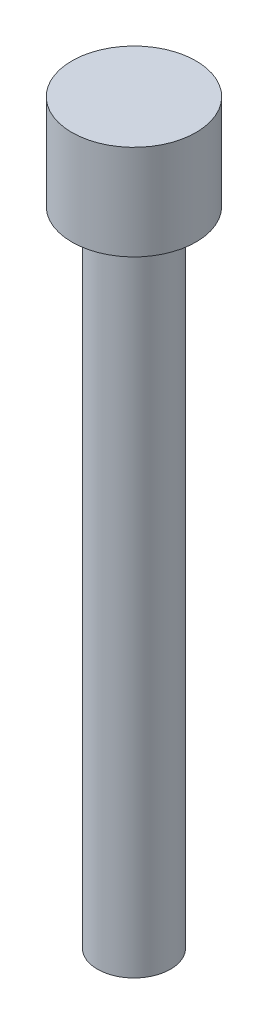
SolidWorks part; units mm, degrees
ref_plane "Front Plane" through (0, 0, 0) normal (0, 0, 1) x (1, 0, 0)
ref_plane "Top Plane" through (0, 0, 0) normal (0, 1, 0) x (1, 0, 0)
ref_plane "Right Plane" through (0, 0, 0) normal (1, 0, 0) x (0, 0, -1)
sketch "Sketch1" plane through (0, 0, 0) normal (0, 1, 0) x (1, 0, 0)
  circle A0 centre (0, 0) radius 2.5
  dimension "D1" = 5
extrude "Boss-Extrude1" add sketch "Sketch1" along normal blind 44
sketch "Sketch2" plane through (0, 44, 0) normal (0, 1, 0) x (1, 0, 0)
  circle A0 centre (0, 0) radius 4.25
  dimension "D1" = 8.5
extrude "Boss-Extrude2" add sketch "Sketch2" along normal blind 6.5
